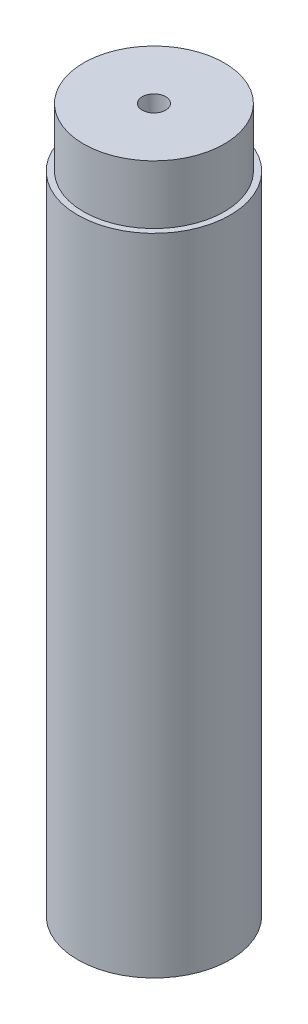
SolidWorks part; units mm, degrees
ref_plane "Front Plane" through (0, 0, 0) normal (0, 0, 1) x (1, 0, 0)
ref_plane "Top Plane" through (0, 0, 0) normal (0, 1, 0) x (1, 0, 0)
ref_plane "Right Plane" through (0, 0, 0) normal (1, 0, 0) x (0, 0, -1)
sketch "Sketch1" plane through (0, 0, 0) normal (0, 1, 0) x (1, 0, 0)
  circle A0 centre (0, 0) radius 32.5
  circle A1 centre (0, 0) radius 5
extrude "Boss-Extrude1" add sketch "Sketch1" along normal blind 300
sketch "Sketch2" plane through (0, 300, 0) normal (0, 1, 0) x (1, 0, 0)
  circle A0 centre (0, 0) radius 32.5
  circle A1 centre (0, 0) radius 30
extrude "Cut-Extrude2" cut sketch "Sketch2" against normal blind 25
